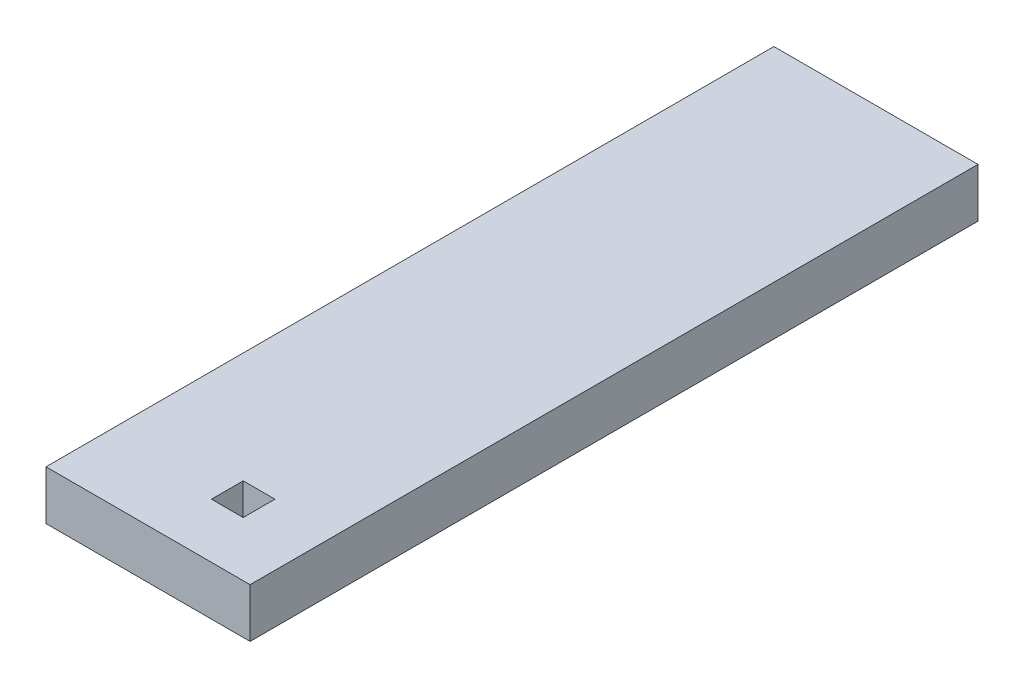
SolidWorks part; units mm, degrees
material "Acrylic (Medium-high impact)"
ref_plane "Front Plane" through (0, 0, 0) normal (0, 0, 1) x (1, 0, 0)
ref_plane "Top Plane" through (0, 0, 0) normal (0, 1, 0) x (1, 0, 0)
ref_plane "Right Plane" through (0, 0, 0) normal (1, 0, 0) x (0, 0, -1)
sketch "Sketch1" plane through (0, 0, 0) normal (0, 1, 0) x (1, 0, 0)
  line L0 (0, -18.9392) -> (0, 0) construction
  line L1 (5, -23.495) -> (-5, -23.495)
  line L2 (5, -23.495) -> (5, 23.495)
  line L3 (5, 23.495) -> (-5, 23.495)
  line L4 (-5, -23.495) -> (-5, 23.495)
  line L5 (5, -23.495) -> (-5, 23.495) construction
  line L6 (5, 23.495) -> (-5, -23.495) construction
  line L7 (-1.025, -17.9142) -> (1.025, -17.9142)
  line L8 (-1.025, -17.9142) -> (-1.025, -19.9642)
  line L9 (-1.025, -19.9642) -> (1.025, -19.9642)
  line L10 (1.025, -17.9142) -> (1.025, -19.9642)
  line L11 (-1.025, -17.9142) -> (1.025, -19.9642) construction
  line L12 (-1.025, -19.9642) -> (1.025, -17.9142) construction
  point P0 (0, 0)
  point P6 (0, -18.9392)
  dimension "D1" = 10
  dimension "D2" = 46.99
  dimension "D3" = 2.05
  dimension "D4" = 3.5308
extrude "Boss-Extrude1" add sketch "Sketch1" along normal blind 3.175
sketch "Sketch2" plane through (0, 3.175, 0) normal (0, 1, 0) x (1, 0, 0)
  line L5 (5, -23.495) -> (-5, -23.495) construction
  line L6 (-5, 23.495) -> (-8.175, 23.495)
  line L7 (-5, 23.495) -> (-5, -23.495)
  line L8 (-5, -23.495) -> (-8.175, -23.495)
  line L9 (-8.175, 23.495) -> (-8.175, -23.495)
  dimension "D1" = 3.175
extrude "Boss-Extrude2" add sketch "Sketch2" against normal up to surface (3.175 mm away) up to face at (0, 0, 0)
equation "\"bottomThickness\"= .220in"
equation "\"wallThickness\"= .125in"
equation "\"D1@Boss-Extrude1\"=\"wallThickness\""
equation "\"D1@Sketch2\"=\"wallThickness\""
